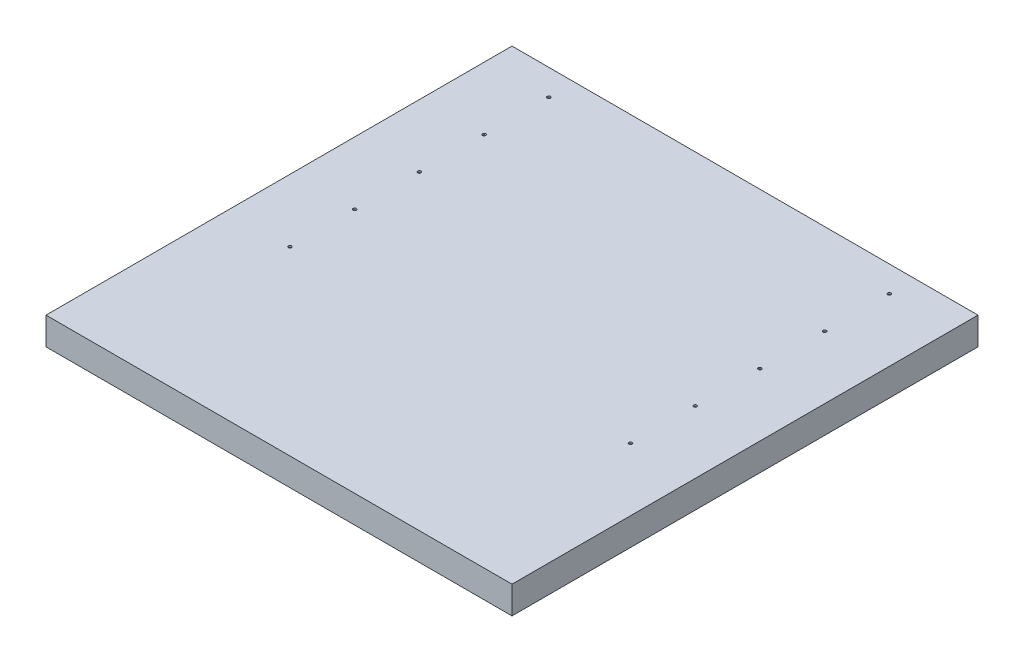
SolidWorks part; units mm, degrees
material "6061 Alloy"
ref_plane "Front Plane" through (0, 0, 0) normal (0, 0, 1) x (1, 0, 0)
ref_plane "Top Plane" through (0, 0, 0) normal (0, 1, 0) x (1, 0, 0)
ref_plane "Right Plane" through (0, 0, 0) normal (1, 0, 0) x (0, 0, -1)
sketch "Sketch1" plane through (0, 0, 0) normal (0, 1, 0) x (1, 0, 0)
  line L0 (0, 0) -> (0, 50000) construction
  line L1 (-457.2, -457.2) -> (457.2, -457.2)
  line L2 (-457.2, -457.2) -> (-457.2, 457.2)
  line L3 (-457.2, 457.2) -> (457.2, 457.2)
  line L4 (457.2, -457.2) -> (457.2, 457.2)
  line L5 (-457.2, -457.2) -> (457.2, 457.2) construction
  line L6 (-457.2, 457.2) -> (457.2, -457.2) construction
  circle A0 centre (-334.137, 406.4) radius 3.175
  circle A1 centre (-334.137, 279.4) radius 3.175
  circle A2 centre (-334.137, 152.4) radius 3.175
  circle A3 centre (-334.137, 25.4) radius 3.175
  circle A4 centre (-334.137, -101.6) radius 3.175
  circle A5 centre (334.137, -101.6) radius 3.175
  circle A6 centre (334.137, 25.4) radius 3.175
  circle A7 centre (334.137, 152.4) radius 3.175
  circle A8 centre (334.137, 279.4) radius 3.175
  circle A9 centre (334.137, 406.4) radius 3.175
  point P0 (0, 0)
  dimension "D5" = 6.35
  dimension "D1" = 914.4
  dimension "D2" = 914.4
  dimension "D3" = 334.137
  dimension "D4" = 50.8
  dimension "D6" = 5
extrude "Boss-Extrude1" add sketch "Sketch1" along normal blind 3.175
sketch "Sketch4" plane through (0, 0, 0) normal (0, -1, 0) x (1, 0, 0)
  line L0 (457.2, 457.2) -> (457.2, -457.2) construction
  line L1 (457.2, -457.2) -> (-457.2, -457.2) construction
  line L2 (-457.2, -457.2) -> (-457.2, 457.2) construction
  line L3 (-457.2, 457.2) -> (457.2, 457.2) construction
  line L4 (457.2, 457.2) -> (457.2, -457.2)
  line L5 (457.2, -457.2) -> (-457.2, -457.2)
  line L6 (-457.2, -457.2) -> (-457.2, 457.2)
  line L7 (-457.2, 457.2) -> (457.2, 457.2)
  line L8 (-454.025, 454.025) -> (454.025, 454.025)
  line L9 (454.025, 454.025) -> (454.025, -454.025)
  line L10 (454.025, -454.025) -> (-454.025, -454.025)
  line L11 (-454.025, -454.025) -> (-454.025, 454.025)
  dimension "D1" = 3.175
extrude "Boss-Extrude2" add sketch "Sketch4" along normal blind 50.8
